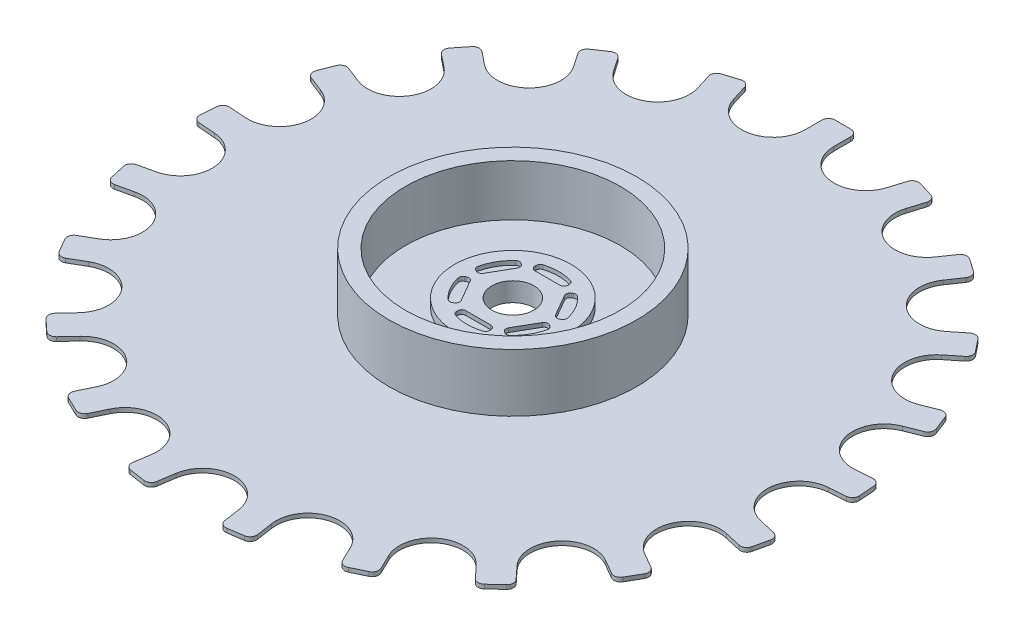
SolidWorks part; units mm, degrees
material "ABS"
ref_plane "Plano frontal" through (0, 0, 0) normal (0, 0, 1) x (1, 0, 0)
ref_plane "Plano superior" through (0, 0, 0) normal (0, 1, 0) x (1, 0, 0)
ref_plane "Plano direito" through (0, 0, 0) normal (1, 0, 0) x (0, 0, -1)
sketch "Esboço1" plane through (0, 0, 0) normal (0, -1, 0) x (1, 0, 0)
  line L0 (-1.745, -0.8) -> (-1.745, 0) construction
  line L1 (-0.945, 0) -> (0.945, 0)
  line L2 (-1.745, -0.8) -> (-1.745, -39.142)
  line L3 (-0.945, -39.942) -> (0.945, -39.942)
  line L4 (1.745, -0.8) -> (1.745, -39.142)
  line L5 (-0.945, 0) -> (-1.745, 0) construction
  arc A0 (0.945, 0) -> (1.745, -0.8) centre (0.945, -0.8) cw
  arc A1 (-0.945, 0) -> (-1.745, -0.8) centre (-0.945, -0.8) ccw
  arc A2 (0.945, -39.942) -> (1.745, -39.142) centre (0.945, -39.142) ccw
  arc A3 (-1.745, -39.142) -> (-0.945, -39.942) centre (-0.945, -39.142) ccw
  point P4 (0, 0)
  point P8 (1.745, 0)
  point P11 (-1.745, 0)
  point P14 (1.745, -39.942)
  dimension "D3" = 0.8
  dimension "D4" = 0.8
  dimension "D1" = 3.49
  dimension "D2" = 39.942
extrude "Ressalto-extrusão1" add sketch "Esboço1" along normal mid plane 0.5
sketch "Esboço2" plane through (0, 0, 0) normal (0, 1, 0) x (1, 0, 0)
  line L0 (-1.745, 0.8) -> (-1.745, 39.142) construction
  circle A0 centre (0, 0) radius 1.745
extrude "Ressalto-extrusão2" add sketch "Esboço2" along normal blind 4.625
pattern_circular "PadrãoCircular1" count 21 over 360 about axis through (0, 0, 0) along (0, 1, 0) of "Ressalto-extrusão1"
fillet "Fillet2" radius 3.85 21 edges at (0, 0, 11.7081) (3.451, 0, 11.1879) (6.5954, 0, 9.6737) (10.8988, 0, 4.2774) (9.1538, 0, 7.2999) (11.6754, 0, 0.8749) (11.4145, 0, -2.6053) (10.1395, 0, -5.854) (7.9635, 0, -8.5826) (5.0799, 0, -10.5486) (1.745, 0, -11.5773) (-1.745, 0, -11.5773) (-5.0799, 0, -10.5486) (-7.9635, 0, -8.5826) (-10.1395, 0, -5.854) (-11.4145, 0, -2.6053) (-11.6754, 0, 0.8749) (-10.8988, 0, 4.2774) (-9.1538, 0, 7.2999) (-6.5954, 0, 9.6737) (-3.451, 0, 11.1879)
sketch "Sketch2" plane through (0, 0.25, 0) normal (0, 1, 0) x (1, 0, 0)
  circle A0 centre (0, 0) radius 15
  dimension "D1" = 30
extrude "Boss-Extrude1" add sketch "Sketch2" along normal blind 7
sketch "Sketch4" plane through (0, 7.25, 0) normal (0, 1, 0) x (1, 0, 0)
  circle A0 centre (0, 0) radius 13
  circle A1 centre (0, 0) radius 15
  circle A2 centre (0, 0) radius 15 construction
  dimension "D1" = 0
  dimension "D2" = 2
extrude "Cut-Extrude2" cut sketch "Sketch4" against normal blind 6.2
sketch "Sketch7" plane through (0, 1.05, 0) normal (0, 1, 0) x (1, 0, 0)
  circle A0 centre (0, 0) radius 6.75 construction
  circle A1 centre (0, 0) radius 7.05
  dimension "D1" = 13.5
  dimension "D2" = 0.3
extrude "Boss-Extrude4" add sketch "Sketch7" along normal blind 1
sketch "Sketch9" plane through (0, 2.05, 0) normal (0, 1, 0) x (1, 0, 0)
  line L0 (-2, -4.8221) -> (-2, -4.6771)
  line L1 (-1.5, -4.1771) -> (1.5, -4.1771)
  line L2 (2, -4.6771) -> (2, -4.8221)
  line L18 (-5.176, -0.679) -> (-5.0505, -0.6065)
  line L19 (-4.3675, -0.7895) -> (-2.8675, -3.3876)
  line L20 (-3.0505, -4.0706) -> (-3.176, -4.1431)
  line L21 (-3.176, 4.1431) -> (-3.0505, 4.0706)
  line L22 (-2.8675, 3.3876) -> (-4.3675, 0.7895)
  line L23 (-5.0505, 0.6065) -> (-5.176, 0.679)
  line L24 (2, 4.8221) -> (2, 4.6771)
  line L25 (1.5, 4.1771) -> (-1.5, 4.1771)
  line L26 (-2, 4.6771) -> (-2, 4.8221)
  line L27 (5.176, 0.679) -> (5.0505, 0.6065)
  line L28 (4.3675, 0.7895) -> (2.8675, 3.3876)
  line L29 (3.0505, 4.0706) -> (3.176, 4.1431)
  line L30 (3.176, -4.1431) -> (3.0505, -4.0706)
  line L31 (2.8675, -3.3876) -> (4.3675, -0.7895)
  line L32 (5.0505, -0.6065) -> (5.176, -0.679)
  circle A1 centre (0, 0) radius 7.05
  circle A2 centre (0, 0) radius 7.05 construction
  circle A5 centre (0, 0) radius 5.55
  arc A6 (-1.6485, -5.2995) -> (1.6485, -5.2995) centre (0, 0) ccw
  arc A9 (2, -4.8221) -> (1.6485, -5.2995) centre (1.5, -4.8221) cw
  arc A10 (-2, -4.8221) -> (-1.6485, -5.2995) centre (-1.5, -4.8221) ccw
  arc A11 (1.5, -4.1771) -> (2, -4.6771) centre (1.5, -4.6771) cw
  arc A12 (-2, -4.6771) -> (-1.5, -4.1771) centre (-1.5, -4.6771) cw
  arc A13 (-5.4138, -1.2221) -> (-3.7653, -4.0774) centre (0, 0) ccw
  arc A14 (-3.176, -4.1431) -> (-3.7653, -4.0774) centre (-3.426, -3.7101) cw
  arc A15 (-5.176, -0.679) -> (-5.4138, -1.2221) centre (-4.926, -1.112) ccw
  arc A16 (-2.8675, -3.3876) -> (-3.0505, -4.0706) centre (-3.3005, -3.6376) cw
  arc A17 (-5.0505, -0.6065) -> (-4.3675, -0.7895) centre (-4.8005, -1.0395) cw
  arc A18 (-3.7653, 4.0774) -> (-5.4138, 1.2221) centre (0, 0) ccw
  arc A19 (-5.176, 0.679) -> (-5.4138, 1.2221) centre (-4.926, 1.112) cw
  arc A20 (-3.176, 4.1431) -> (-3.7653, 4.0774) centre (-3.426, 3.7101) ccw
  arc A21 (-4.3675, 0.7895) -> (-5.0505, 0.6065) centre (-4.8005, 1.0395) cw
  arc A22 (-3.0505, 4.0706) -> (-2.8675, 3.3876) centre (-3.3005, 3.6376) cw
  arc A23 (1.6485, 5.2995) -> (-1.6485, 5.2995) centre (0, 0) ccw
  arc A24 (-2, 4.8221) -> (-1.6485, 5.2995) centre (-1.5, 4.8221) cw
  arc A25 (2, 4.8221) -> (1.6485, 5.2995) centre (1.5, 4.8221) ccw
  arc A26 (-1.5, 4.1771) -> (-2, 4.6771) centre (-1.5, 4.6771) cw
  arc A27 (2, 4.6771) -> (1.5, 4.1771) centre (1.5, 4.6771) cw
  arc A28 (5.4138, 1.2221) -> (3.7653, 4.0774) centre (0, 0) ccw
  arc A29 (3.176, 4.1431) -> (3.7653, 4.0774) centre (3.426, 3.7101) cw
  arc A30 (5.176, 0.679) -> (5.4138, 1.2221) centre (4.926, 1.112) ccw
  arc A31 (2.8675, 3.3876) -> (3.0505, 4.0706) centre (3.3005, 3.6376) cw
  arc A32 (5.0505, 0.6065) -> (4.3675, 0.7895) centre (4.8005, 1.0395) cw
  arc A33 (3.7653, -4.0774) -> (5.4138, -1.2221) centre (0, 0) ccw
  arc A34 (5.176, -0.679) -> (5.4138, -1.2221) centre (4.926, -1.112) cw
  arc A35 (3.176, -4.1431) -> (3.7653, -4.0774) centre (3.426, -3.7101) ccw
  arc A36 (4.3675, -0.7895) -> (5.0505, -0.6065) centre (4.8005, -1.0395) cw
  arc A37 (3.0505, -4.0706) -> (2.8675, -3.3876) centre (3.3005, -3.6376) cw
  point P6 (0, -4.1771)
  point P35 (-2, -5.1771)
  point P38 (2, -4.1771)
  point P41 (-2, -4.1771)
  point P84 (0, 0)
  dimension "D6" = 0.5
  dimension "D3" = 1
  dimension "D4" = 4
  dimension "D1" = 0
  dimension "D2" = 1.5
extrude "Cut-Extrude3" cut sketch "Sketch9" against normal blind 0.5
sketch "Sketch3" plane through (0, 0, 0) normal (0, 1, 0) x (1, 0, 0)
  circle A0 centre (0, 0) radius 2 construction
  circle A1 centre (0, 0) radius 2.55
  dimension "D1" = 4
  dimension "D2" = 0.55
extrude "Cut-Extrude1" cut sketch "Sketch3" against normal through all both and the other way through all
